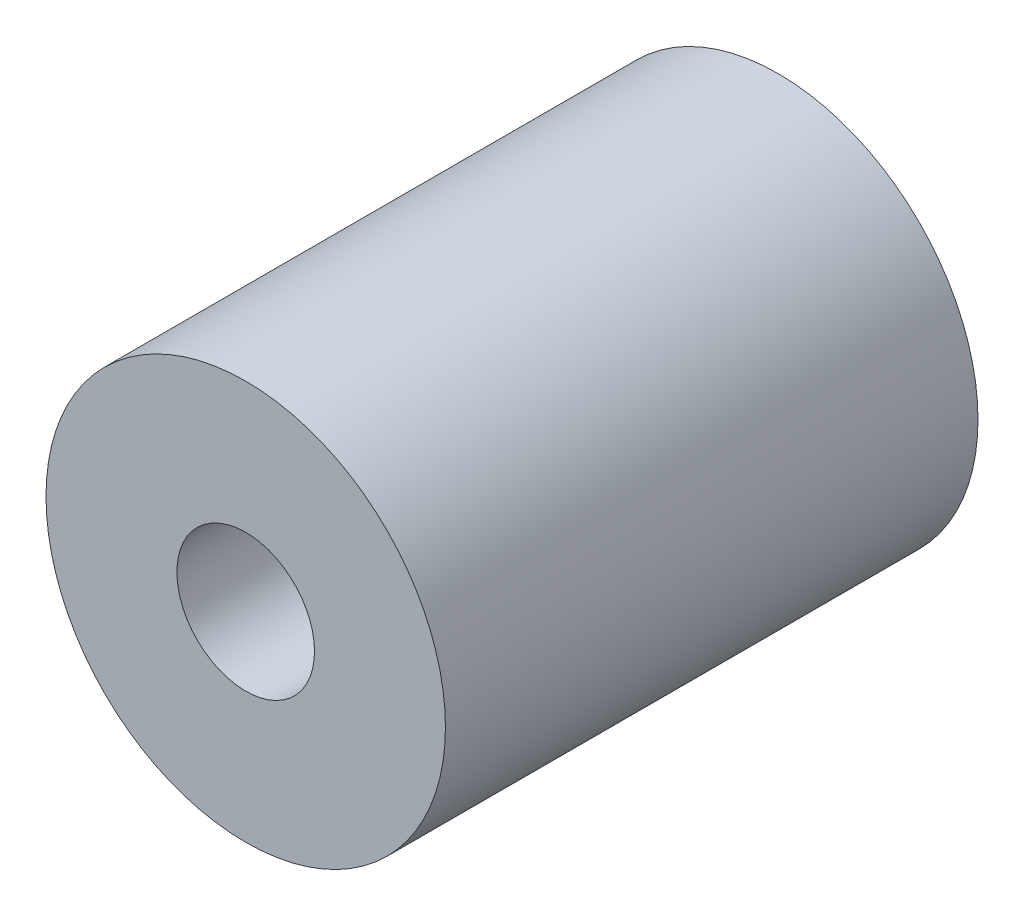
SolidWorks part; units mm, degrees
ref_plane "Front Plane" through (0, 0, 0) normal (0, 0, 1) x (1, 0, 0)
ref_plane "Top Plane" through (0, 0, 0) normal (0, 1, 0) x (1, 0, 0)
ref_plane "Right Plane" through (0, 0, 0) normal (1, 0, 0) x (0, 0, -1)
sketch "Sketch1" plane through (0, 0, 0) normal (0, 0, 1) x (1, 0, 0)
  circle A0 centre (0, 0) radius 3.1
  circle A1 centre (0, 0) radius 9
  dimension "D1" = 18
  dimension "D2" = 6.2
extrude "Boss-Extrude1" add sketch "Sketch1" along normal blind 24
